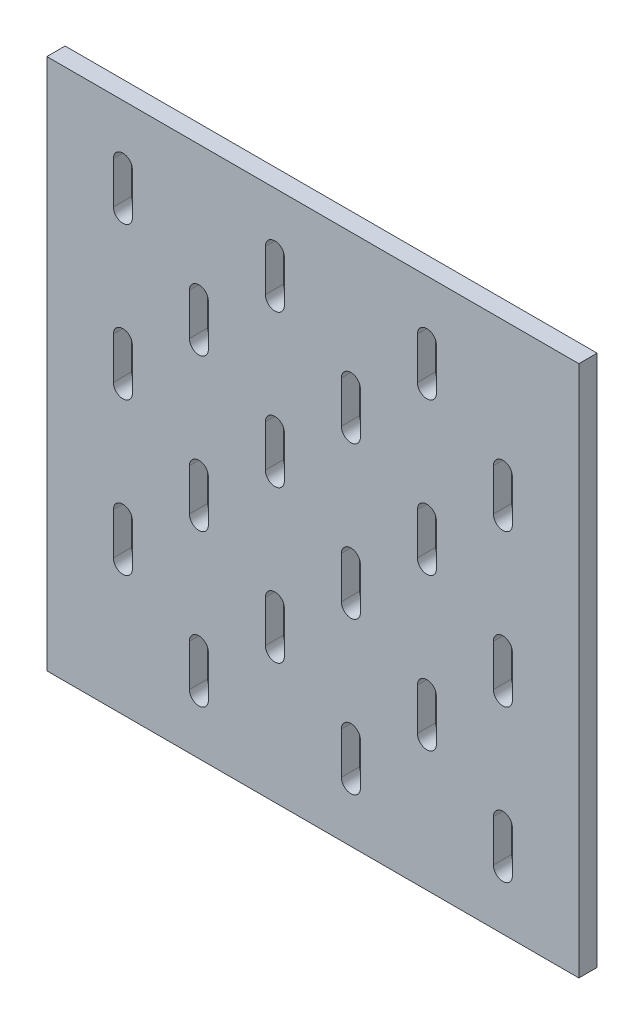
SolidWorks part; units mm, degrees
ref_plane "Спереди" through (0, 0, 0) normal (0, 0, 1) x (1, 0, 0)
ref_plane "Сверху" through (0, 0, 0) normal (0, 1, 0) x (1, 0, 0)
ref_plane "Справа" through (0, 0, 0) normal (1, 0, 0) x (0, 0, -1)
sketch "Эскиз1" plane through (0, 0, 0) normal (0, 0, 1) x (1, 0, 0)
  line L0 (0, 13.75) -> (0, -13.75) construction
  line L1 (6.25, 13.75) -> (6.25, -13.75)
  line L2 (-6.25, 13.75) -> (-6.25, -13.75)
  line L3 (-50, 63.75) -> (-50, 36.25) construction
  line L4 (-43.75, 63.75) -> (-43.75, 36.25)
  line L5 (-56.25, 63.75) -> (-56.25, 36.25)
  line L6 (100, -30.7884) -> (100, 36.25) construction
  line L7 (100, 13.75) -> (100, -13.75) construction
  line L10 (0, -30.7884) -> (0, 36.25) construction
  line L11 (106.25, 13.75) -> (106.25, -13.75)
  line L19 (93.75, 13.75) -> (93.75, -13.75)
  line L22 (50, 63.75) -> (50, 36.25) construction
  line L23 (56.25, 63.75) -> (56.25, 36.25)
  line L24 (43.75, 63.75) -> (43.75, 36.25)
  line L27 (200, -30.7884) -> (200, 36.25) construction
  line L30 (200, 13.75) -> (200, -13.75) construction
  line L33 (206.25, 13.75) -> (206.25, -13.75)
  line L34 (193.75, 13.75) -> (193.75, -13.75)
  line L35 (150, 63.75) -> (150, 36.25) construction
  line L36 (156.25, 63.75) -> (156.25, 36.25)
  line L37 (143.75, 63.75) -> (143.75, 36.25)
  line L38 (100, 69.2116) -> (100, 136.25) construction
  line L39 (100, 113.75) -> (100, 86.25) construction
  line L40 (106.25, 113.75) -> (106.25, 86.25)
  line L41 (93.75, 113.75) -> (93.75, 86.25)
  line L42 (50, 163.75) -> (50, 136.25) construction
  line L43 (56.25, 163.75) -> (56.25, 136.25)
  line L44 (43.75, 163.75) -> (43.75, 136.25)
  line L45 (200, 69.2116) -> (200, 136.25) construction
  line L46 (200, 113.75) -> (200, 86.25) construction
  line L47 (206.25, 113.75) -> (206.25, 86.25)
  line L48 (193.75, 113.75) -> (193.75, 86.25)
  line L49 (150, 163.75) -> (150, 136.25) construction
  line L50 (156.25, 163.75) -> (156.25, 136.25)
  line L51 (143.75, 163.75) -> (143.75, 136.25)
  line L52 (100, 169.2116) -> (100, 236.25) construction
  line L53 (100, 213.75) -> (100, 186.25) construction
  line L54 (106.25, 213.75) -> (106.25, 186.25)
  line L55 (93.75, 213.75) -> (93.75, 186.25)
  line L56 (50, 263.75) -> (50, 236.25) construction
  line L57 (56.25, 263.75) -> (56.25, 236.25)
  line L58 (43.75, 263.75) -> (43.75, 236.25)
  line L59 (200, 169.2116) -> (200, 236.25) construction
  line L60 (200, 213.75) -> (200, 186.25) construction
  line L61 (206.25, 213.75) -> (206.25, 186.25)
  line L62 (193.75, 213.75) -> (193.75, 186.25)
  line L63 (150, 263.75) -> (150, 236.25) construction
  line L64 (156.25, 263.75) -> (156.25, 236.25)
  line L65 (143.75, 263.75) -> (143.75, 236.25)
  line L66 (0, 69.2116) -> (0, 136.25) construction
  line L67 (0, 113.75) -> (0, 86.25) construction
  line L68 (6.25, 113.75) -> (6.25, 86.25)
  line L69 (-6.25, 113.75) -> (-6.25, 86.25)
  line L70 (-50, 163.75) -> (-50, 136.25) construction
  line L71 (-43.75, 163.75) -> (-43.75, 136.25)
  line L72 (-56.25, 163.75) -> (-56.25, 136.25)
  line L73 (0, 169.2116) -> (0, 236.25) construction
  line L74 (0, 213.75) -> (0, 186.25) construction
  line L75 (6.25, 213.75) -> (6.25, 186.25)
  line L76 (-6.25, 213.75) -> (-6.25, 186.25)
  line L77 (-50, 263.75) -> (-50, 236.25) construction
  line L78 (-43.75, 263.75) -> (-43.75, 236.25)
  line L79 (-56.25, 263.75) -> (-56.25, 236.25)
  line L81 (-100, -50) -> (250, -50)
  line L82 (-100, -50) -> (-100, 300)
  line L83 (-100, 300) -> (250, 300)
  line L84 (250, -50) -> (250, 300)
  arc A0 (6.25, 13.75) -> (-6.25, 13.75) centre (0, 13.75) ccw
  arc A1 (-6.25, -13.75) -> (6.25, -13.75) centre (0, -13.75) ccw
  arc A2 (-43.75, 63.75) -> (-56.25, 63.75) centre (-50, 63.75) ccw
  arc A3 (-56.25, 36.25) -> (-43.75, 36.25) centre (-50, 36.25) ccw
  arc A18 (106.25, 13.75) -> (93.75, 13.75) centre (100, 13.75) ccw
  arc A19 (93.75, -13.75) -> (106.25, -13.75) centre (100, -13.75) ccw
  arc A20 (56.25, 63.75) -> (43.75, 63.75) centre (50, 63.75) ccw
  arc A21 (43.75, 36.25) -> (56.25, 36.25) centre (50, 36.25) ccw
  arc A22 (206.25, 13.75) -> (193.75, 13.75) centre (200, 13.75) ccw
  arc A23 (193.75, -13.75) -> (206.25, -13.75) centre (200, -13.75) ccw
  arc A24 (156.25, 63.75) -> (143.75, 63.75) centre (150, 63.75) ccw
  arc A25 (143.75, 36.25) -> (156.25, 36.25) centre (150, 36.25) ccw
  arc A26 (106.25, 113.75) -> (93.75, 113.75) centre (100, 113.75) ccw
  arc A27 (93.75, 86.25) -> (106.25, 86.25) centre (100, 86.25) ccw
  arc A28 (56.25, 163.75) -> (43.75, 163.75) centre (50, 163.75) ccw
  arc A29 (43.75, 136.25) -> (56.25, 136.25) centre (50, 136.25) ccw
  arc A30 (206.25, 113.75) -> (193.75, 113.75) centre (200, 113.75) ccw
  arc A31 (193.75, 86.25) -> (206.25, 86.25) centre (200, 86.25) ccw
  arc A32 (156.25, 163.75) -> (143.75, 163.75) centre (150, 163.75) ccw
  arc A33 (143.75, 136.25) -> (156.25, 136.25) centre (150, 136.25) ccw
  arc A34 (106.25, 213.75) -> (93.75, 213.75) centre (100, 213.75) ccw
  arc A35 (93.75, 186.25) -> (106.25, 186.25) centre (100, 186.25) ccw
  arc A36 (56.25, 263.75) -> (43.75, 263.75) centre (50, 263.75) ccw
  arc A37 (43.75, 236.25) -> (56.25, 236.25) centre (50, 236.25) ccw
  arc A38 (206.25, 213.75) -> (193.75, 213.75) centre (200, 213.75) ccw
  arc A39 (193.75, 186.25) -> (206.25, 186.25) centre (200, 186.25) ccw
  arc A40 (156.25, 263.75) -> (143.75, 263.75) centre (150, 263.75) ccw
  arc A41 (143.75, 236.25) -> (156.25, 236.25) centre (150, 236.25) ccw
  arc A42 (6.25, 113.75) -> (-6.25, 113.75) centre (0, 113.75) ccw
  arc A43 (-6.25, 86.25) -> (6.25, 86.25) centre (0, 86.25) ccw
  arc A44 (-43.75, 163.75) -> (-56.25, 163.75) centre (-50, 163.75) ccw
  arc A45 (-56.25, 136.25) -> (-43.75, 136.25) centre (-50, 136.25) ccw
  arc A46 (6.25, 213.75) -> (-6.25, 213.75) centre (0, 213.75) ccw
  arc A47 (-6.25, 186.25) -> (6.25, 186.25) centre (0, 186.25) ccw
  arc A48 (-43.75, 263.75) -> (-56.25, 263.75) centre (-50, 263.75) ccw
  arc A49 (-56.25, 236.25) -> (-43.75, 236.25) centre (-50, 236.25) ccw
  point P3 (0, 0)
  point P8 (-50, 50)
  point P20 (100, 0)
  point P25 (50, 50)
  point P38 (200, 0)
  point P43 (150, 50)
  point P54 (100, 100)
  point P59 (50, 150)
  point P70 (200, 100)
  point P75 (150, 150)
  point P86 (100, 200)
  point P91 (50, 250)
  point P102 (200, 200)
  point P107 (150, 250)
  point P118 (0, 100)
  point P123 (-50, 150)
  point P134 (0, 200)
  point P139 (-50, 250)
  point P149 (-120.7439, -88.8415)
  point P150 (0, 0)
  dimension "D1" = 40
  dimension "D2" = 12.5
  dimension "D3" = 50
  dimension "D4" = 50
  dimension "D7" = 100
  dimension "D8" = 100
  dimension "D9" = 100
  dimension "D10" = 50
  dimension "D11" = 50
  dimension "D12" = 50
  dimension "D5" = 3
  dimension "D6" = 3
extrude "Бобышка-Вытянуть1" add sketch "Эскиз1" along normal blind 12 contours L81 L84 L83 L82 A49 L79 A48 L78 A47 L76 A46 L75 A45 L72 A44 L71 A43 L69 A42 L68 A41 L65 A40 L64 A39 L62 A38 L61 A37 L58 A36 L57 A35 L55 A34 L54 A33 L51 A32 L50 A31
